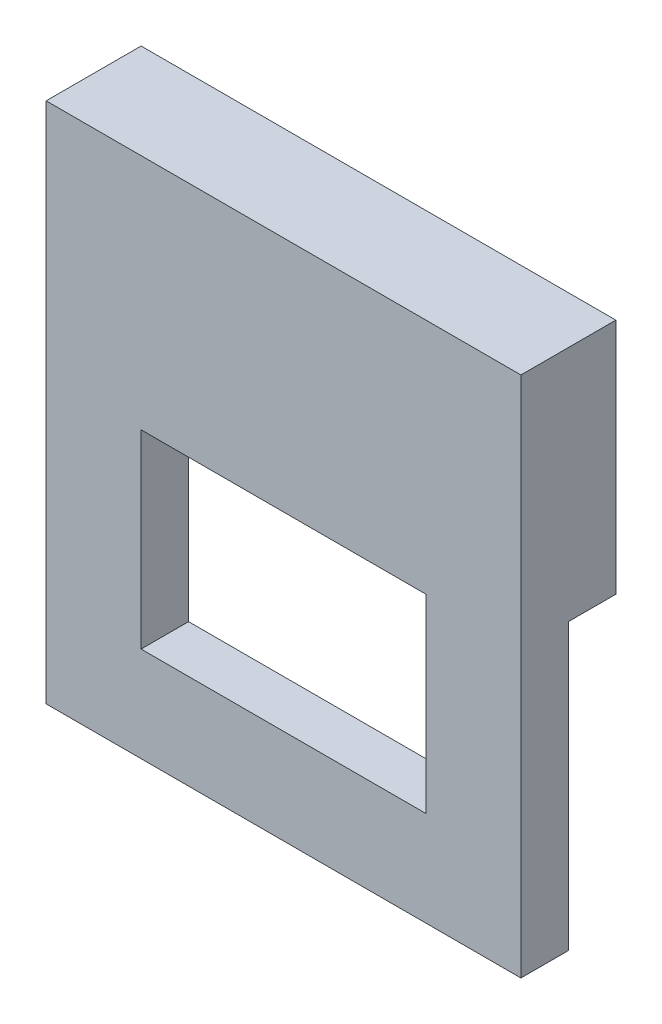
SolidWorks part; units mm, degrees
ref_plane "Ebene vorne" through (0, 0, 0) normal (0, 0, 1) x (1, 0, 0)
ref_plane "Ebene oben" through (0, 0, 0) normal (0, 1, 0) x (1, 0, 0)
ref_plane "Ebene rechts" through (0, 0, 0) normal (1, 0, 0) x (0, 0, -1)
sketch "Skizze1" plane through (0, 0, 0) normal (1, 0, 0) x (0, 0, -1)
  line L0 (0, 0) -> (1, 0)
  line L1 (1, 0) -> (1, 5)
  line L2 (1, 5) -> (-1, 5)
  line L3 (-1, 5) -> (-1, -6)
  line L4 (-1, -6) -> (0, -6)
  line L5 (0, -6) -> (0, 0)
  dimension "D1" = 1
  dimension "D2" = 5
  dimension "D3" = 6
extrude "Linear austragen1" add sketch "Skizze1" along normal mid plane 10
sketch "Skizze2" plane through (0, 0, 1) normal (0, 0, 1) x (1, 0, 0)
  line L0 (-3, 0) -> (-5, 0) construction
  line L1 (-3, 0) -> (3, 0)
  line L2 (-3, 0) -> (-3, -4)
  line L3 (-3, -4) -> (3, -4)
  line L4 (3, 0) -> (3, -4)
  line L5 (-5, 5) -> (-5, -6) construction
  line L6 (3, 0) -> (5, 0) construction
  line L7 (5, 5) -> (5, -6) construction
  line L8 (5, -6) -> (-5, -6) construction
  dimension "D1" = 6
  dimension "D2" = 4
  dimension "D3" = 2
extrude "Linear austragen2" cut sketch "Skizze2" against normal blind 10
